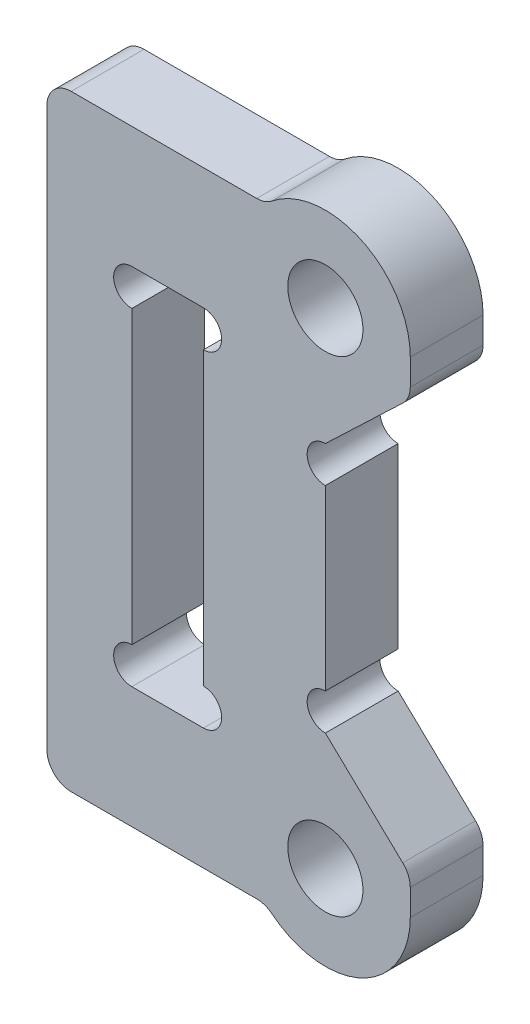
SolidWorks part; units mm, degrees
ref_plane "前视基准面" through (0, 0, 0) normal (0, 0, 1) x (1, 0, 0)
ref_plane "上视基准面" through (0, 0, 0) normal (0, 1, 0) x (1, 0, 0)
ref_plane "右视基准面" through (0, 0, 0) normal (1, 0, 0) x (0, 0, -1)
sketch "草图1" plane through (0, 0, 0) normal (0, 0, 1) x (1, 0, 0)
  line L0 (0, -10) -> (0, 10) construction
  line L1 (27.5, 10) -> (27.5, -10) construction
  line L2 (-2.4495, 12.5) -> (-11.475, 12.5)
  line L3 (-5.025, -7.5) -> (-7.975, -7.5)
  line L4 (-5.025, -7.5) -> (-5.025, 7.5)
  line L5 (-5.025, 7.5) -> (-7.975, 7.5)
  line L6 (-7.975, -7.5) -> (-7.975, 7.5)
  line L7 (-5.025, -7.5) -> (-7.975, 7.5) construction
  line L8 (-5.025, 7.5) -> (-7.975, -7.5) construction
  line L9 (-11.475, 12.5) -> (-11.475, -12.5)
  line L10 (-11.475, -12.5) -> (-2.4495, -12.5)
  line L11 (3.5, 10) -> (3.5, -10)
  circle A0 centre (0, 10) radius 1.55
  circle A1 centre (0, -10) radius 1.55
  arc A2 (-2.4495, -12.5) -> (3.5, -10) centre (0, -10) ccw
  arc A3 (3.5, 10) -> (-2.4495, 12.5) centre (0, 10) ccw
  point P3 (-11.475, 0)
  point P4 (0, 0)
  point P10 (27.5, 0)
  point P11 (-6.5, 0)
  dimension "D1" = 3.1
  dimension "D7" = 7
  dimension "D2" = 20
  dimension "D3" = 27.5
  dimension "D4" = 15
  dimension "D5" = 2.95
  dimension "D6" = 68
  dimension "D8" = 5
  dimension "D9" = 3.5
extrude "凸台-拉伸1" add sketch "草图1" along normal mid plane 3
fillet "圆角1" radius 1 2 edges at (-11.475, -12.5, 0) (-11.475, 12.5, 0)
sketch "草图2" plane through (0, 0, 1.5) normal (0, 0, 1) x (1, 0, 0)
  line L0 (-7.975, 7.5) -> (-7.975, -7.5) construction
  line L1 (-5.025, -7.5) -> (-5.025, 7.5) construction
  circle A0 centre (-7.975, 6.75) radius 0.75
  circle A1 centre (-5.025, 6.75) radius 0.75
  circle A2 centre (-7.975, -6.75) radius 0.75
  circle A3 centre (-5.025, -6.75) radius 0.75
  dimension "D1" = 1.5
extrude "切除-拉伸1" cut sketch "草图2" against normal through all
sketch "草图3" plane through (0, 0, 1.5) normal (0, 0, 1) x (1, 0, 0)
  line L0 (3.5, 8.5) -> (0, 5.1667)
  line L1 (3.5, -10) -> (3.5, 10) construction
  line L2 (0, 5.1667) -> (0, -5.1667)
  line L3 (0, -5.1667) -> (3.5, -8.5)
  line L4 (3.5, -8.5) -> (3.5, 8.5)
  circle A0 centre (0, 10) radius 1.55 construction
  point P6 (3.5, 0)
  point P7 (0, 0)
  dimension "D1" = 3.5
  dimension "D2" = 17
  dimension "D3" = 3.5
extrude "切除-拉伸2" cut sketch "草图3" against normal through all
sketch "草图4" plane through (0, 0, 1.5) normal (0, 0, 1) x (1, 0, 0)
  line L0 (0, 5.1667) -> (0, -5.1667) construction
  circle A0 centre (0, 4.4167) radius 0.75
  circle A1 centre (0, -4.4167) radius 0.75
  dimension "D1" = 1.5
extrude "切除-拉伸3" cut sketch "草图4" against normal through all
fillet "圆角2" radius 1 4 edges at (-2.4495, -12.5, 0) (3.5, -8.5, 0) (3.5, 8.5, 0) (-2.4495, 12.5, 0)
